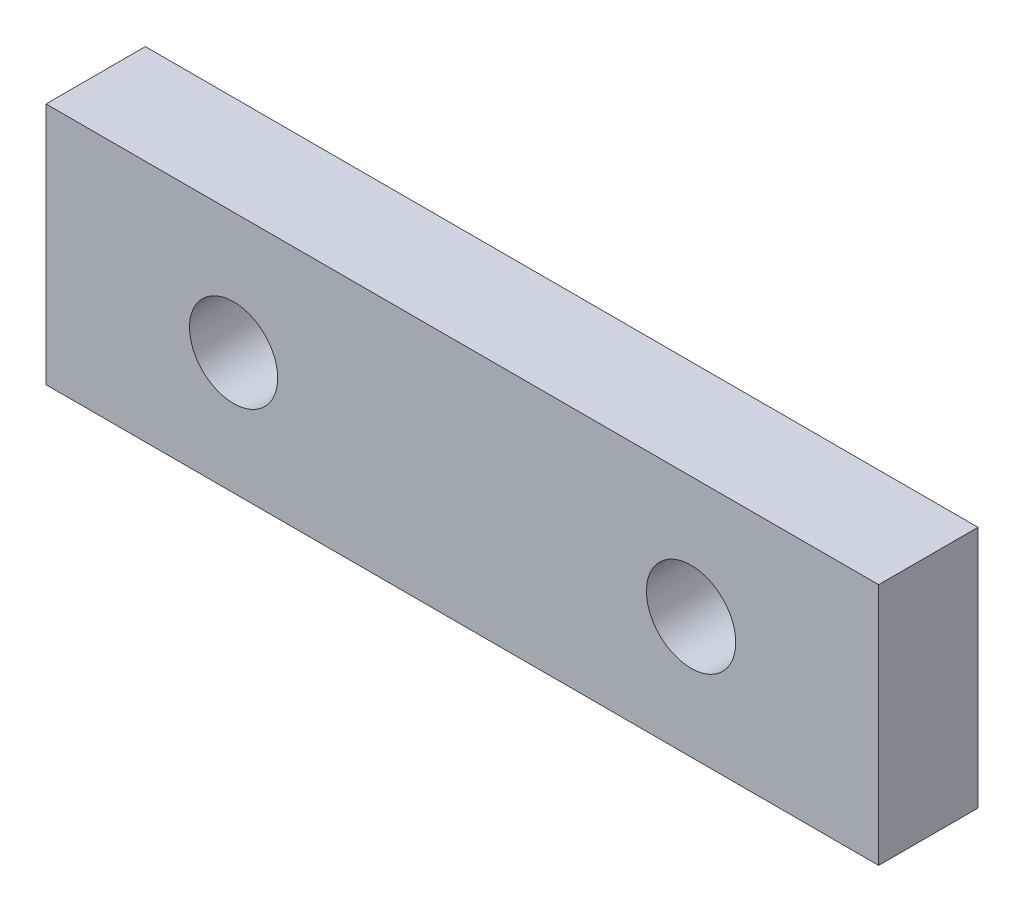
SolidWorks part; units mm, degrees
ref_plane "Front Plane" through (0, 0, 0) normal (0, 0, 1) x (1, 0, 0)
ref_plane "Top Plane" through (0, 0, 0) normal (0, 1, 0) x (1, 0, 0)
ref_plane "Right Plane" through (0, 0, 0) normal (1, 0, 0) x (0, 0, -1)
sketch "Sketch1" plane through (0, 0, 0) normal (0, 0, 1) x (1, 0, 0)
  line L1 (-40.4495, 11.811) -> (40.4495, 11.811)
  line L2 (-40.4495, 11.811) -> (-40.4495, -11.811)
  line L3 (-40.4495, -11.811) -> (40.4495, -11.811)
  line L4 (40.4495, 11.811) -> (40.4495, -11.811)
  line L5 (-40.4495, 11.811) -> (40.4495, -11.811) construction
  line L6 (-40.4495, -11.811) -> (40.4495, 11.811) construction
  circle A0 centre (-22.225, 0) radius 4.2833
  circle A1 centre (22.225, 0) radius 4.3377
  point P0 (0, 0)
  dimension "D1" = 80.899
  dimension "D2" = 23.622
  dimension "D3" = 22.225
  dimension "D4" = 22.225
extrude "Boss-Extrude1" add sketch "Sketch1" along normal blind 9.652
